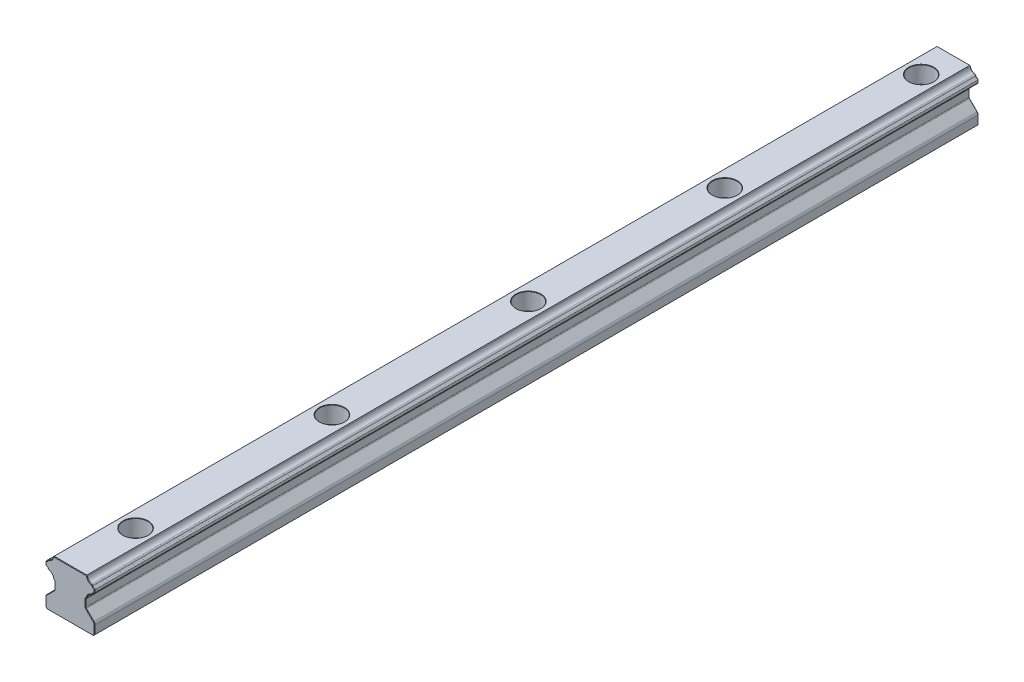
SolidWorks part; units mm, degrees
material "Plain Carbon Steel"
ref_plane "Front Plane" through (0, 0, 0) normal (0, 0, 1) x (1, 0, 0)
ref_plane "Top Plane" through (0, 0, 0) normal (0, 1, 0) x (1, 0, 0)
ref_plane "Right Plane" through (0, 0, 0) normal (1, 0, 0) x (0, 0, -1)
sketch "Rail Profile" plane through (0, 0, 0) normal (0, 0, 1) x (1, 0, 0)
  line L47 (0, 0) -> (0, 20) construction
  line L48 (-7, 0) -> (7, 0)
  line L49 (7, 0) -> (7.5, 0.5)
  line L50 (7.5, 0.5) -> (7.5, 3.0858)
  line L58 (7.2071, 3.7929) -> (4.8672, 6.1328)
  line L59 (4.75, 6.4157) -> (4.75, 8.5843)
  line L60 (4.8672, 8.8672) -> (5.063, 9.063)
  line L61 (7.5, 11.6657) -> (7.5, 12.3343)
  line L62 (-7, 0) -> (-7.5, 0.5)
  line L63 (5, 15) -> (-5, 15)
  line L64 (6.75, 9) -> (6.75, 15) construction
  line L65 (5.063, 14.937) -> (5, 15)
  line L66 (-7.5, 0.5) -> (-7.5, 3.0858)
  line L67 (6.75, 15) -> (3.75, 12) construction
  line L68 (3.75, 12) -> (6.75, 9) construction
  line L69 (7.1, 12.3343) -> (7.1, 11.6657) construction
  line L70 (6.4042, 13.0301) -> (6.4042, 10.9699) construction
  line L71 (-7.2071, 3.7929) -> (-4.8672, 6.1328)
  line L72 (-4.75, 6.4157) -> (-4.75, 8.5843)
  line L73 (-4.8672, 8.8672) -> (-5.063, 9.063)
  line L74 (5, 15) -> (8, 12) construction
  line L75 (4.8672, 8.8672) -> (8, 12) construction
  line L76 (-7.5, 11.6657) -> (-7.5, 12.3343)
  line L77 (-5.063, 14.937) -> (-5, 15)
  arc A4 (6.4734, 13.4241) -> (5.1741, 14.7234) centre (6.75, 15) cw
  arc A6 (5.1741, 9.2766) -> (6.4734, 10.5759) centre (6.75, 9) cw
  arc A7 (7.2071, 3.7929) -> (7.5, 3.0858) centre (6.5, 3.0858) cw
  arc A8 (5.063, 14.937) -> (5.1741, 14.7234) centre (4.7801, 14.6542) cw
  arc A9 (6.4734, 13.4241) -> (6.8012, 13.0792) centre (6.4042, 13.0301) cw
  arc A10 (7.1491, 12.7313) -> (7.5, 12.3343) centre (7.1, 12.3343) cw
  arc A11 (7.5, 11.6657) -> (7.1491, 11.2687) centre (7.1, 11.6657) cw
  arc A12 (6.8012, 10.9208) -> (6.4734, 10.5759) centre (6.4042, 10.9699) cw
  arc A13 (5.1741, 9.2766) -> (5.063, 9.063) centre (4.7801, 9.3458) cw
  arc A14 (4.8672, 8.8672) -> (4.75, 8.5843) centre (5.15, 8.5843) ccw
  arc A15 (4.75, 6.4157) -> (4.8672, 6.1328) centre (5.15, 6.4157) ccw
  arc A16 (6.8012, 13.0792) -> (7.1491, 12.7313) centre (7.1981, 13.1283) ccw
  arc A17 (7.1491, 11.2687) -> (6.8012, 10.9208) centre (7.1981, 10.8717) ccw
  arc A18 (-7.2071, 3.7929) -> (-7.5, 3.0858) centre (-6.5, 3.0858) ccw
  arc A19 (-4.75, 6.4157) -> (-4.8672, 6.1328) centre (-5.15, 6.4157) cw
  arc A20 (-4.8672, 8.8672) -> (-4.75, 8.5843) centre (-5.15, 8.5843) cw
  arc A21 (-5.1741, 9.2766) -> (-5.063, 9.063) centre (-4.7801, 9.3458) ccw
  arc A22 (-5.1741, 9.2766) -> (-6.4734, 10.5759) centre (-6.75, 9) ccw
  arc A23 (-6.8012, 10.9208) -> (-6.4734, 10.5759) centre (-6.4042, 10.9699) ccw
  arc A24 (-7.1491, 11.2687) -> (-6.8012, 10.9208) centre (-7.1981, 10.8717) cw
  arc A25 (-7.5, 11.6657) -> (-7.1491, 11.2687) centre (-7.1, 11.6657) ccw
  arc A26 (-7.1491, 12.7313) -> (-7.5, 12.3343) centre (-7.1, 12.3343) ccw
  arc A27 (-6.8012, 13.0792) -> (-7.1491, 12.7313) centre (-7.1981, 13.1283) cw
  arc A28 (-6.4734, 13.4241) -> (-6.8012, 13.0792) centre (-6.4042, 13.0301) ccw
  arc A29 (-6.4734, 13.4241) -> (-5.1741, 14.7234) centre (-6.75, 15) ccw
  arc A30 (-5.063, 14.937) -> (-5.1741, 14.7234) centre (-4.7801, 14.6542) ccw
  point P2 (4.75, 7.5)
  point P12 (7.5, 12)
  point P19 (6.75, 12)
  point P25 (5.1578, 14.8422)
  point P50 (8, 12)
  point P78 (0, 15)
  dimension "Rb" = 1.6
  dimension "Rf1" = 1
  dimension "Rf2" = 0.4
  dimension "WR" = 15
  dimension "Wi" = 9.5
  dimension "Wt" = 5
  dimension "Ac" = 135
  dimension "HR" = 15
  dimension "Hm" = 7.5
  dimension "Hb" = 12
  dimension "Hc" = 0.5
  dimension "Wb" = 7.5
extrude "Body" add sketch "Rail Profile" against normal blind 270
chamfer "Aesthetic Chamfer" distance 0.15 angle 45 84 edges at (-5.0315, 14.9685, 0) (-5.135, 14.8388, 0) (-5.6186, 13.8686, 0) (-6.6941, 13.3057, 0) (-6.9153, 12.8454, 0) (-7.3997, 12.5992, 0) (-7.5, 12, 0) (-7.3997, 11.4008, 0) (-6.9153, 11.1546, 0) (-6.6941, 10.6943, 0) (-5.6186, 10.1314, 0) (-5.135, 9.1612, 0) (-4.9651, 8.9651, 0) (-4.7804, 8.7374, 0) (-4.75, 7.5, 0) (-4.7804, 6.2626, 0) (-6.0371, 4.9629, 0) (-7.4239, 3.4685, 0) (-7.5, 1.7929, 0) (-7.25, 0.25, 0) (0, 0, 0) (7.25, 0.25, 0) (5.0315, 14.9685, 0) (5.135, 14.8388, 0) (5.6186, 13.8686, 0) (6.6941, 13.3057, 0) (6.9153, 12.8454, 0) (7.3997, 12.5992, 0) (7.5, 12, 0) (7.3997, 11.4008, 0) (6.9153, 11.1546, 0) (6.6941, 10.6943, 0) (5.6186, 10.1314, 0) (5.135, 9.1612, 0) (4.9651, 8.9651, 0) (4.7804, 8.7374, 0) (7.5, 1.7929, 0) (4.75, 7.5, 0) (7.4239, 3.4685, 0) (4.7804, 6.2626, 0) (6.0371, 4.9629, 0) (0, 15, 0) (5.0315, 14.9685, -270) (5.135, 14.8388, -270) (5.6186, 13.8686, -270) (6.6941, 13.3057, -270) (6.9153, 12.8454, -270) (7.3997, 12.5992, -270) (7.5, 12, -270) (7.3997, 11.4008, -270) (6.9153, 11.1546, -270) (6.6941, 10.6943, -270) (5.6186, 10.1314, -270) (5.135, 9.1612, -270) (4.9651, 8.9651, -270) (4.7804, 8.7374, -270) (4.75, 7.5, -270) (4.7804, 6.2626, -270) (6.0371, 4.9629, -270) (7.4239, 3.4685, -270) (7.5, 1.7929, -270) (7.25, 0.25, -270) (0, 0, -270) (-7.25, 0.25, -270) (-5.0315, 14.9685, -270) (-5.135, 14.8388, -270) (-5.6186, 13.8686, -270) (-6.6941, 13.3057, -270) (-6.9153, 12.8454, -270) (-7.3997, 12.5992, -270) (-7.5, 12, -270) (-7.3997, 11.4008, -270) (-6.9153, 11.1546, -270) (-6.6941, 10.6943, -270) (-5.6186, 10.1314, -270) (-7.5, 1.7929, -270) (-5.135, 9.1612, -270) (-7.4239, 3.4685, -270) (-4.9651, 8.9651, -270) (-6.0371, 4.9629, -270) (-4.7804, 8.7374, -270) (-4.7804, 6.2626, -270) (-4.75, 7.5, -270) (0, 15, -270)
hole_wizard "Mounting Hole" positions "3DSketch1" profile "Sketch1" counterbore size "M4" standard "ISO" end condition through all
sketch3d "3DSketch1"
  point P0 (0, 15, -20)
  dimension "D1" = 7.5
  dimension "E1" = 20
sketch "Sketch1" plane through (0, 15, -20) normal (1, 0, 0) x (0, 0, 1)
  line L0 (0, 0) -> (0, 15)
  line L1 (2.25, 14.9) -> (2.35, 15)
  line L2 (2.25, 14.9) -> (2.25, 5.4)
  line L3 (2.25, 5.4) -> (2.35, 5.3)
  line L4 (2.35, 5.3) -> (3.75, 5.3)
  line L5 (3.75, 5.3) -> (3.75, 0.1)
  line L6 (3.75, 0.1) -> (3.85, 0)
  line L7 (3.85, 0) -> (0, 0)
  line L8 (-3.75, 0.1) -> (-3.85, 0) construction
  line L9 (-2.25, 5.4) -> (-2.35, 5.3) construction
  line L11 (0, -6.35) -> (0, 107.95) construction
  line L12 (2.35, 15) -> (0, 15)
  line L13 (-2.25, 14.9) -> (-2.35, 15) construction
  dimension "Thru Hole Dia." = 4.5
  dimension "Thru Hole Depth" = 15
  dimension "C'Bore Dia." = 7.5
  dimension "C'Bore Depth" = 5.3
  dimension "Near C'Sink Dia." = 7.7
  dimension "Near C'Sink Angle" = 90
  dimension "Mid C'Sink Dia." = 4.7
  dimension "Mid C'Sink Angle" = 90
  dimension "Far C'Sink Dia." = 4.7
  dimension "Far C'Sink Angle" = 90
fillet "Production Fillet" radius 0.1 1 edges at (0, 9.7, -16.25)
pattern_linear "Mounting Holes Pattern" count 5 spacing 60 along (0, 0, -1) of "Mounting Hole", "Production Fillet"
equation "\"Wt@Rail Profile\"= \"WR@Rail Profile\" / 3'Top Side Half Width"
equation "\"Hm@Rail Profile\"= \"HR@Rail Profile\" / 2'Recirculation Avoidance Height"
equation "\"Hb@Rail Profile\"= 0.8 * \"HR@Rail Profile\"'Pivot Height"
equation "\"Hc@Rail Profile\"= \"WR@Rail Profile\" / 30'Chamfer Width"
equation "\"Wb@Rail Profile\"= \"WR@Rail Profile\" / 2'Ball Center Cross Width"
equation "\"D1@3DSketch1\"= \"WR@Rail Profile\" / 2'Hole Center Position"
